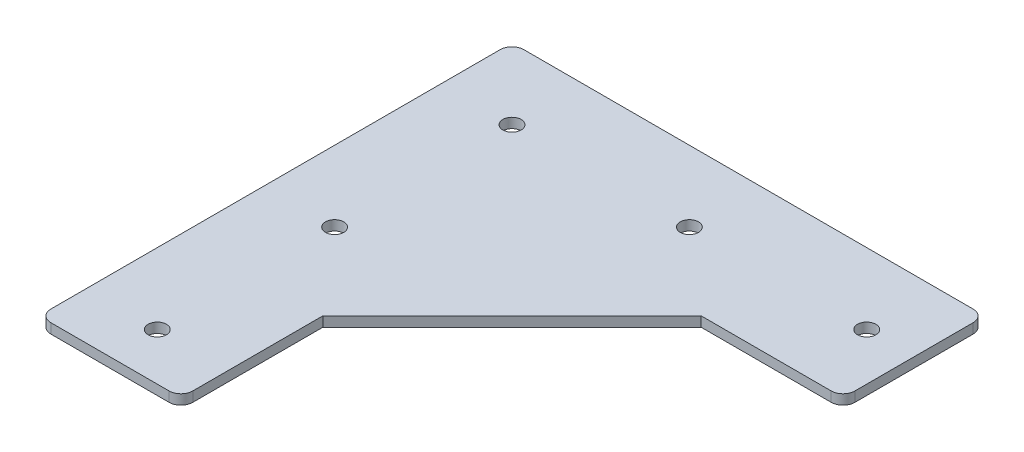
SolidWorks part; units mm, degrees
material "Plain Carbon Steel"
ref_plane "Front Plane" through (0, 0, 0) normal (0, 0, 1) x (1, 0, 0)
ref_plane "Top Plane" through (0, 0, 0) normal (0, 1, 0) x (1, 0, 0)
ref_plane "Right Plane" through (0, 0, 0) normal (1, 0, 0) x (0, 0, -1)
sketch "Sketch1" plane through (0, 0, 0) normal (0, 1, 0) x (1, 0, 0)
  line L0 (0, 0) -> (38.1, 0)
  line L1 (0, 0) -> (38.1, 0)
  line L2 (0, 0) -> (0, 127)
  line L3 (0, 127) -> (88.9, 127)
  line L5 (88.9, 88.9) -> (38.1, 38.1)
  line L6 (38.1, 0) -> (38.1, 38.1)
  line L7 (88.9, 88.9) -> (127, 88.9)
  line L8 (127, 88.9) -> (127, 127)
  line L9 (127, 127) -> (88.9, 127)
  dimension "D1" = 127
  dimension "D2" = 127
  dimension "D3" = 38.1
  dimension "D4" = 38.1
  dimension "D5" = 38.1
  dimension "D6" = 38.1
extrude "Boss-Extrude1" add sketch "Sketch1" along normal blind 2.6568 contours L8 L9 L3 L2 L0 L6 L5 L7
hole_wizard "#10 (0.1935) Diameter Hole1" positions "Sketch2" profile "Sketch3" hole size "#10" standard "ANSI Inch" end condition through all
sketch "Sketch2" plane through (0, 2.6568, 0) normal (0, 1, 0) x (1, 0, 0)
  line L0 (127, 107.95) -> (0, 107.95) construction
  line L1 (127, 88.9) -> (127, 127) construction
  line L2 (0, 0) -> (0, 127) construction
  line L4 (19.05, 0) -> (19.05, 129.7764) construction
  line L5 (0, 0) -> (38.1, 0) construction
  point P0 (114.3, 107.95)
  point P2 (66.675, 107.95)
  point P6 (19.05, 107.95)
  point P8 (19.05, 60.325)
  point P10 (19.05, 12.7)
  dimension "D1" = 12.7
  dimension "D2" = 12.7
  dimension "D3" = 47.625
  dimension "D4" = 47.625
  dimension "D6" = 47.625
  dimension "D5" = 47.625
sketch "Sketch3" plane through (114.3, 2.6568, -107.95) normal (1, 0, 0) x (0, 0, 1)
  line L0 (0, 0) -> (0, 2.6568)
  line L1 (0, 2.6568) -> (2.4574, 2.6568)
  line L2 (2.4574, 2.6568) -> (2.4574, 0)
  line L5 (2.4574, 0) -> (0, 0)
  line L11 (0, -6.35) -> (0, 107.95) construction
  dimension "Thru Hole Dia." = 4.9149
  dimension "Thru Hole Depth" = 2.6568
fillet "Fillet1" radius 3.175 5 edges at (0, 1.3284, -127) (127, 1.3284, -127) (127, 1.3284, -88.9) (0, 1.3284, 0) (38.1, 1.3284, 0)
equation "\"D2@Sketch2\"=\"D1@Sketch2\""
